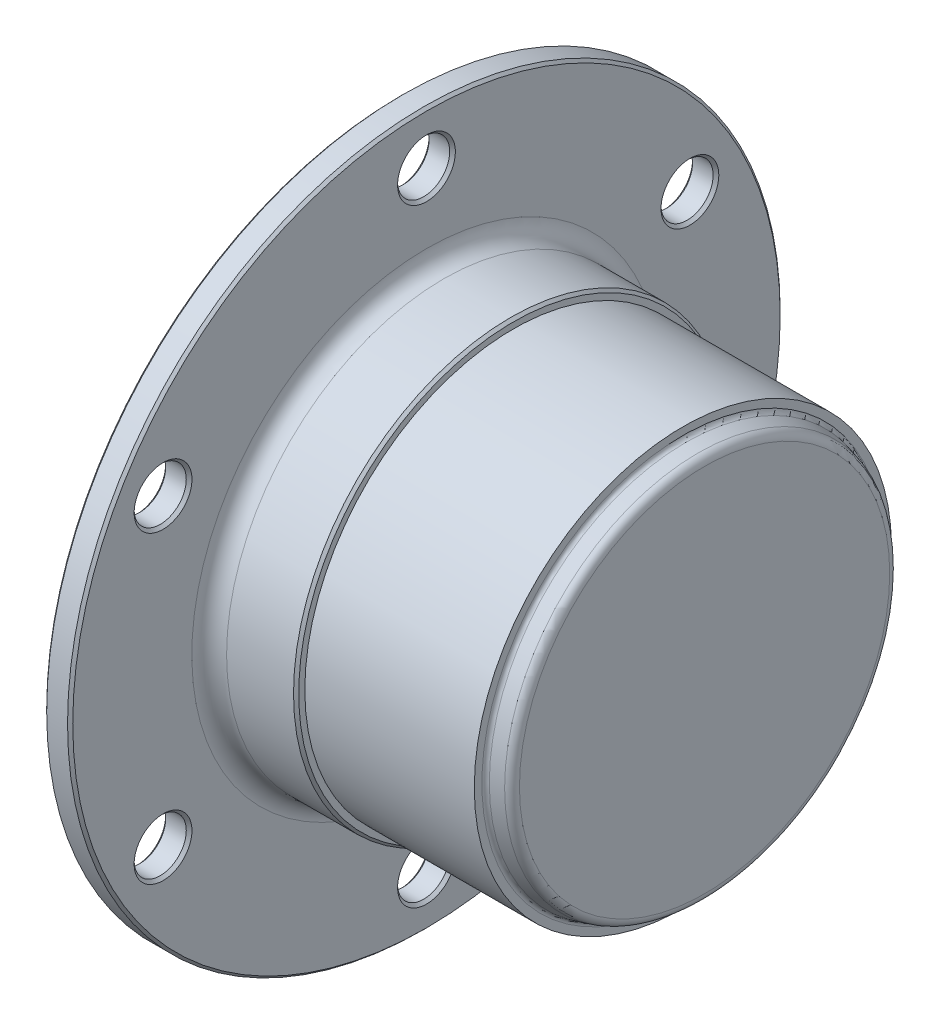
SolidWorks part; units mm, degrees
ref_plane "Front Plane" through (0, 0, 0) normal (0, 0, 1) x (1, 0, 0)
ref_plane "Top Plane" through (0, 0, 0) normal (0, 1, 0) x (1, 0, 0)
ref_plane "Right Plane" through (0, 0, 0) normal (1, 0, 0) x (0, 0, -1)
sketch "Sketch1" plane through (0, 0, 0) normal (0, 0, 1) x (1, 0, 0)
  line L0 (0, 41) -> (0, 0)
  line L1 (0, 0) -> (5, 0)
  line L2 (5, 0) -> (5, 25)
  line L3 (3, 27) -> (3, 41)
  line L4 (3, 41) -> (0, 41)
  line L5 (0, 0) -> (5, 0) construction
  arc A0 (5, 25) -> (3, 27) centre (5, 27) cw
  dimension "D1" = 2
  dimension "D2" = 25
  dimension "D3" = 41
revolve "Revolve1" add sketch "Sketch1" angle 360 about L5
sketch "Sketch2" plane through (5, 0, 0) normal (1, 0, 0) x (0, 0, -1)
  circle A0 centre (0, 0) radius 25
extrude "Boss-Extrude1" add sketch "Sketch2" along normal blind 7.7
sketch "Sketch3" plane through (12.7, 0, 0) normal (1, 0, 0) x (0, 0, -1)
  circle A0 centre (0, 0) radius 25
extrude "Boss-Extrude2" add sketch "Sketch3" along normal blind 0.3 draft 45
sketch "Sketch4" plane through (13, 0, 0) normal (1, 0, 0) x (0, 0, -1)
  circle A0 centre (0, 0) radius 24
extrude "Boss-Extrude3" add sketch "Sketch4" along normal blind 19.5
sketch "Sketch5" plane through (32.5, 0, 0) normal (1, 0, 0) x (0, 0, -1)
  circle A0 centre (0, 0) radius 22.7411
extrude "Boss-Extrude4" add sketch "Sketch5" along normal blind 2.5 draft 15.027
hole_wizard "Ø6.0 (6) Diameter Hole1" positions "Sketch7" profile "Sketch6" hole size "Ø6.0" standard "ANSI Metric"
sketch "Sketch7" plane through (3, 0, 0) normal (1, 0, 0) x (0, 0, -1)
  circle A0 centre (0, 0) radius 35
  point P0 (-30.3109, -17.5)
  point P1 (-30.3109, 17.5)
  point P2 (0, 35)
  point P3 (30.3109, 17.5)
  point P4 (30.3109, -17.5)
  point P5 (0, -35)
  point P10 (0, 0)
  point P11 (0, 0)
  point P12 (0, 0)
  point P13 (0, 0)
  point P14 (0, 0)
  dimension "D1" = 35
sketch "Sketch6" plane through (3, -17.5, 30.3109) normal (0, 1, 0) x (0, 0, -1)
  line L0 (0, 0) -> (0, 3)
  line L1 (0, 3) -> (3, 3)
  line L2 (3, 3) -> (3, 0.3269)
  line L3 (3, 0.3269) -> (3.3269, 0)
  line L5 (3.3269, 0) -> (0, 0)
  line L6 (-3, 0.3269) -> (-3.3269, 0) construction
  line L11 (0, -6.35) -> (0, 107.95) construction
  dimension "Thru Hole Dia." = 6
  dimension "Thru Hole Depth" = 3
  dimension "Near C'Sink Dia." = 6.6538
  dimension "Near C'Sink Angle" = 90
chamfer "Chamfer1" distance 0.3 angle 45 8 edges at (0, 35, -3) (0, -17.5, -33.3109) (0, 17.5, 27.3109) (0, 17.5, -33.3109) (0, -35, -3) (3, 41, 0) (0, 41, 0) (0, -17.5, 27.3109)
fillet "Fillet1" radius 0.5 1 edges at (32.5, 0, -22.7411)
fillet "Fillet2" radius 1 1 edges at (35, 0, -22.07)
